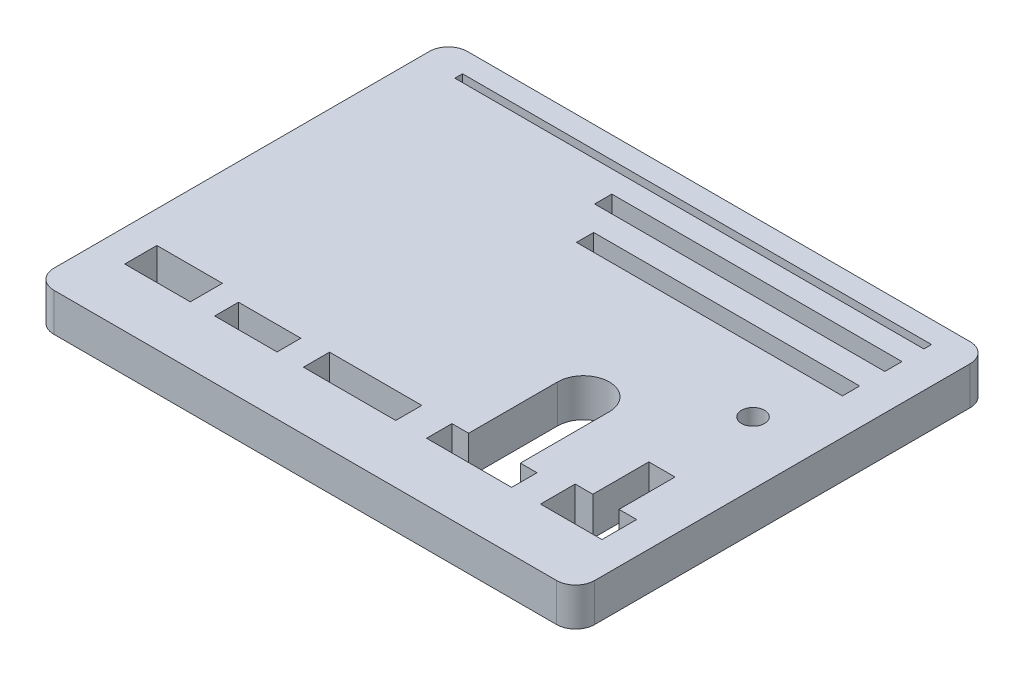
SolidWorks part; units mm, degrees
ref_plane "Front Plane" through (0, 0, 0) normal (0, 0, 1) x (1, 0, 0)
ref_plane "Top Plane" through (0, 0, 0) normal (0, 1, 0) x (1, 0, 0)
ref_plane "Right Plane" through (0, 0, 0) normal (1, 0, 0) x (0, 0, -1)
sketch "Sketch1" plane through (0, 0, 0) normal (0, 1, 0) x (1, 0, 0)
  line L0 (52.5378, -23.3598) -> (-72.7778, -23.3598) construction
  line L1 (-42.5, -32.5) -> (42.5, -32.5)
  line L2 (-42.5, -32.5) -> (-42.5, 32.5)
  line L3 (-42.5, 32.5) -> (42.5, 32.5)
  line L4 (42.5, -32.5) -> (42.5, 32.5)
  line L5 (-42.5, -32.5) -> (42.5, 32.5) construction
  line L6 (-42.5, 32.5) -> (42.5, -32.5) construction
  line L7 (9.2325, -19.3698) -> (24.0025, -19.3698) construction
  line L8 (37.5, -23.3598) -> (27.84, -23.3598)
  line L9 (37.5, -23.3598) -> (37.5, -17.9098)
  line L10 (37.5, -17.9098) -> (34.73, -17.9098)
  line L11 (27.84, -23.3598) -> (27.84, -17.9098)
  line L16 (23.3025, -23.3598) -> (9.9325, -23.3598)
  line L17 (23.3025, -23.3598) -> (23.3025, -19.3698)
  line L18 (23.3025, -19.3698) -> (20.6825, -19.3698)
  line L19 (9.9325, -23.3598) -> (9.9325, -19.3698)
  line L20 (5.085, -23.3598) -> (-9.415, -23.3598)
  line L21 (5.085, -23.3598) -> (5.085, -19.2598)
  line L22 (5.085, -19.2598) -> (-9.415, -19.2598)
  line L23 (-9.415, -23.3598) -> (-9.415, -19.2598)
  line L24 (-13.5625, -23.3598) -> (-23.3625, -23.3598)
  line L25 (-13.5625, -23.3598) -> (-13.5625, -19.6198)
  line L26 (-13.5625, -19.6198) -> (-23.3625, -19.6198)
  line L27 (-23.3625, -23.3598) -> (-23.3625, -19.6198)
  line L28 (-27.2, -23.3598) -> (-37.5, -23.3598)
  line L29 (-27.2, -23.3598) -> (-27.2, -18.3098)
  line L30 (-27.2, -18.3098) -> (-37.5, -18.3098)
  line L31 (-37.5, -23.3598) -> (-37.5, -18.3098)
  line L32 (-9.725, -19.2598) -> (5.395, -19.2598) construction
  line L33 (-23.3625, -19.6198) -> (-27.2, -19.6198) construction
  line L34 (-9.725, -19.2598) -> (-13.5625, -19.2598) construction
  line L35 (5.395, -18.3098) -> (9.2325, -18.3098) construction
  line L36 (24.0025, -18.7084) -> (27.84, -18.7084) construction
  line L37 (-2.165, -19.2598) -> (-2.165, -3.2598) construction
  line L39 (30.61, -17.9098) -> (30.61, -9.1098)
  line L40 (30.61, -9.1098) -> (34.73, -9.1098)
  line L41 (34.73, -17.9098) -> (34.73, -9.1098)
  line L42 (-32.35, -18.3098) -> (-32.35, 23.6902) construction
  line L43 (-36.85, 29.0733) -> (36.85, 29.0733)
  line L44 (-36.85, 29.0733) -> (-36.85, 27.8733)
  line L45 (-36.85, 27.8733) -> (36.85, 27.8733)
  line L46 (36.85, 29.0733) -> (36.85, 27.8733)
  line L47 (-36.85, 29.0733) -> (36.85, 27.8733) construction
  line L48 (-36.85, 27.8733) -> (36.85, 29.0733) construction
  line L49 (36.85, 23.0862) -> (-5.15, 23.0862) construction
  line L50 (36.85, 21.7362) -> (-5.15, 21.7362) construction
  line L51 (36.85, 24.4362) -> (-5.15, 24.4362) construction
  line L52 (-5.15, 23.0862) -> (36.85, 23.0862) construction
  line L53 (36.85, 16.4345) -> (-5.15, 16.4345) construction
  line L54 (36.85, 15.0845) -> (-5.15, 15.0845) construction
  line L55 (36.85, 17.7845) -> (-5.15, 17.7845) construction
  line L56 (-5.15, 16.4345) -> (36.85, 16.4345) construction
  line L57 (30.61, -17.9098) -> (27.84, -17.9098)
  line L58 (12.5525, -19.3698) -> (12.5525, -5.3948)
  line L59 (-8.75, 21.7362) -> (36.85, 21.7362)
  line L60 (-8.75, 21.7362) -> (-8.75, 24.4362)
  line L61 (-8.75, 24.4362) -> (36.85, 24.4362)
  line L62 (36.85, 21.7362) -> (36.85, 24.4362)
  line L63 (-8.75, 21.7362) -> (36.85, 24.4362) construction
  line L64 (-8.75, 24.4362) -> (36.85, 21.7362) construction
  line L65 (-4.95, 15.0845) -> (36.85, 15.0845)
  line L66 (-4.95, 15.0845) -> (-4.95, 17.7845)
  line L67 (-4.95, 17.7845) -> (36.85, 17.7845)
  line L68 (36.85, 15.0845) -> (36.85, 17.7845)
  line L69 (-4.95, 15.0845) -> (36.85, 17.7845) construction
  line L70 (-4.95, 17.7845) -> (36.85, 15.0845) construction
  line L71 (20.6825, -5.3948) -> (20.6825, -19.3698)
  line L72 (16.6175, -1.3298) -> (29.0054, -1.3298) construction
  line L73 (12.5525, -19.3698) -> (9.9325, -19.3698)
  circle A0 centre (32.67, 5.2063) radius 1.81
  arc A1 (36.85, 21.7362) -> (36.85, 24.4362) centre (36.85, 23.0862) ccw construction
  arc A2 (-5.15, 24.4362) -> (-5.15, 21.7362) centre (-5.15, 23.0862) ccw construction
  arc A3 (36.85, 15.0845) -> (36.85, 17.7845) centre (36.85, 16.4345) ccw construction
  arc A4 (-5.15, 17.7845) -> (-5.15, 15.0845) centre (-5.15, 16.4345) ccw construction
  arc A5 (12.5525, -5.3948) -> (20.6825, -5.3948) centre (16.6175, -5.3948) cw
  point P0 (0, 0)
  point P12 (16.6175, -19.3698)
  point P14 (-2.165, -19.2598)
  point P34 (52.5378, -26.5888)
  point P36 (32.67, -23.3598)
  point P42 (32.67, -9.1098)
  point P45 (0, 28.4733)
  point P56 (15.85, 23.0862)
  point P62 (15.95, 16.4345)
  point P69 (15.85, 16.4345)
  point P81 (14.05, 23.0862)
  point P86 (37.5, -23.3598)
  point P88 (16.6175, -23.3598)
  dimension "D26" = 3.62
  dimension "D29" = 8.13
  dimension "D1" = 85
  dimension "D2" = 65
  dimension "D3" = 5.05
  dimension "D4" = 10.3
  dimension "D5" = 9.8
  dimension "D6" = 3.74
  dimension "D7" = 4.1
  dimension "D8" = 14.5
  dimension "D9" = 3.99
  dimension "D10" = 13.37
  dimension "D11" = 5.45
  dimension "D12" = 9.66
  dimension "D13" = 5
  dimension "D14" = 5
  dimension "D15" = 14.77
  dimension "D16" = 15.12
  dimension "D17" = 8.8
  dimension "D18" = 4.12
  dimension "D19" = 16
  dimension "D20" = 73.7
  dimension "D21" = 1.2
  dimension "D22" = 42
  dimension "D23" = 2.7
  dimension "D24" = 42
  dimension "D25" = 2.7
  dimension "D27" = 45.6
  dimension "D28" = 41.8
  dimension "D30" = 18.04
extrude "Boss-Extrude1" add sketch "Sketch1" along normal blind 6
fillet "Fillet1" radius 3 4 edges at (-42.5, 3, -32.5) (42.5, 3, 32.5) (42.5, 3, -32.5) (-42.5, 3, 32.5)
hole_wizard "Ø1.0mm Dowel Hole1" [suppressed] positions "Sketch2" profile "Sketch3" hole size "Ø1.0" standard "ANSI Metric"
sketch "Sketch2" plane through (0, 6, 0) normal (0, 1, 0) x (1, 0, 0)
  point P0 (-7, 0)
  point P2 (-21, 0)
  point P4 (-33, 0)
  dimension "D1" = 7
  dimension "D2" = 14
  dimension "D3" = 12
sketch "Sketch3" plane through (-7, 6, 0) normal (1, 0, 0) x (0, 0, 1)
  line L0 (0, 0) -> (0, 6)
  line L1 (0, 6) -> (1.1, 6)
  line L2 (1.1, 6) -> (1.1, 0)
  line L5 (1.1, 0) -> (0, 0)
  line L11 (0, -6.35) -> (0, 107.95) construction
  dimension "Thru Hole Dia." = 2.2
  dimension "Thru Hole Depth" = 6
mirror "Mirror1" [suppressed] about plane through (0, 0, 0) normal (1, 0, 0)
